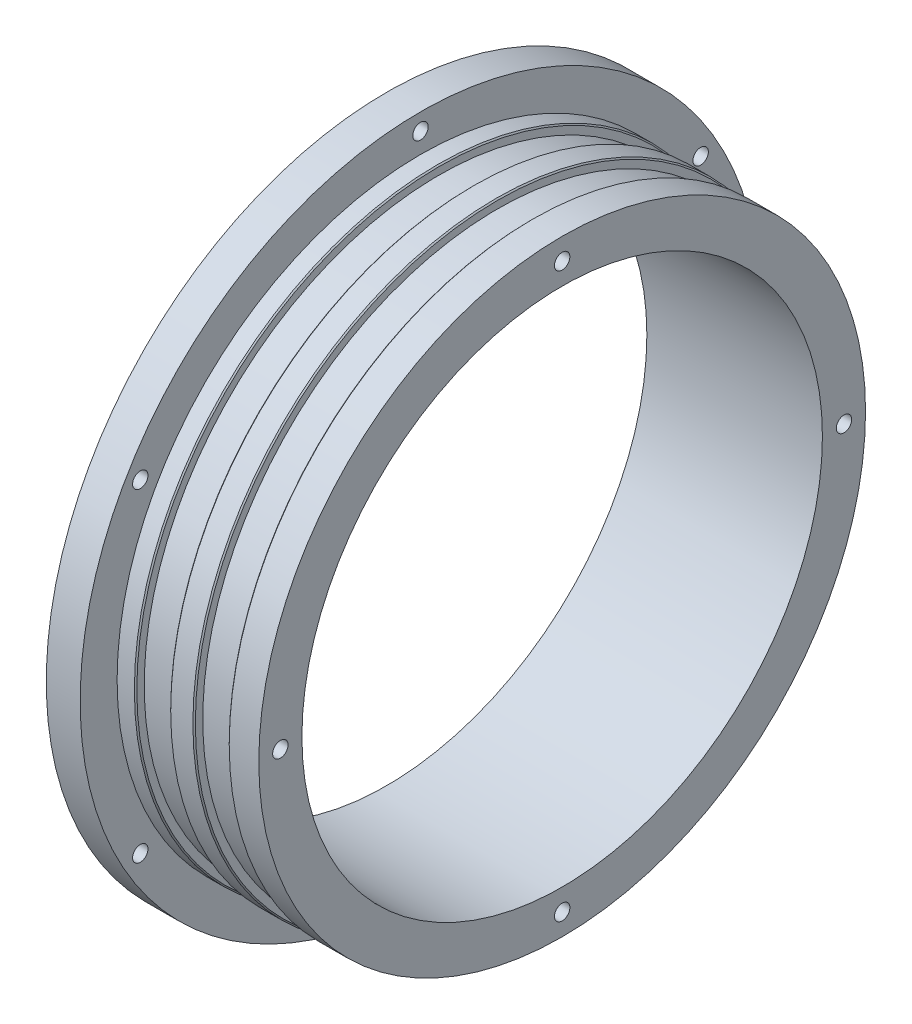
SolidWorks part; units mm, degrees
ref_plane "前视" through (0, 0, 0) normal (0, 0, 1) x (1, 0, 0)
ref_plane "上视" through (0, 0, 0) normal (0, 1, 0) x (1, 0, 0)
ref_plane "右视" through (0, 0, 0) normal (1, 0, 0) x (0, 0, -1)
sketch "草图2" plane through (0, 0, 0) normal (0, 1, 0) x (1, 0, 0)
  line L0 (0, 0) -> (-79.2417, 0) construction
  line L1 (-77.681, 55.25) -> (-72.181, 55.25)
  line L2 (-72.181, 55.25) -> (-72.181, 49.25)
  line L3 (-72.181, 49.25) -> (-69.181, 49.25)
  line L4 (-69.181, 49.25) -> (-69.181, 47.85)
  line L5 (-69.181, 47.85) -> (-63.681, 47.85)
  line L6 (-63.681, 47.85) -> (-63.681, 49.25)
  line L7 (-63.681, 49.25) -> (-59.681, 49.25)
  line L8 (-59.681, 49.25) -> (-59.681, 47.85)
  line L9 (-59.681, 47.85) -> (-54.181, 47.85)
  line L10 (-54.181, 47.85) -> (-54.181, 49.25)
  line L11 (-54.181, 49.25) -> (-49.181, 49.25)
  line L12 (-49.181, 49.25) -> (-49.181, 42.25)
  line L13 (-49.181, 42.25) -> (-77.681, 42.25)
  line L14 (-77.681, 42.25) -> (-77.681, 46.2)
  line L15 (-77.681, 46.2) -> (-76.781, 46.2)
  line L16 (-76.781, 46.2) -> (-76.781, 49.8)
  line L17 (-76.781, 49.8) -> (-77.681, 49.8)
  line L18 (-77.681, 49.8) -> (-77.681, 55.25)
  dimension "D1" = 5.5
  dimension "D2" = 28.5
  dimension "D3" = 6
  dimension "D4" = 1.4
  dimension "D5" = 1.4
  dimension "D6" = 1.4
  dimension "D7" = 1.4
  dimension "D8" = 5.5
  dimension "D9" = 5.5
  dimension "D10" = 3
  dimension "D11" = 4
  dimension "D12" = 5
  dimension "D13" = 0.9
  dimension "D14" = 3.6
  dimension "D15" = 5.45
  dimension "D16" = 49.25
  dimension "D17" = 55.25
  dimension "D18" = 7
  dimension "D19" = 42.25
  dimension "D20" = 3.95
revolve "旋转1" add sketch "草图2" angle 360 about L0
chamfer "倒角1" distance 0.2 angle 45 6 edges at (-77.681, 0, -46.2) (-77.681, 0, -49.8) (-69.181, 0, -49.25) (-63.681, 0, -49.25) (-59.681, 0, -49.25) (-54.181, 0, -49.25)
sketch "草图3" plane through (-49.181, 0, 0) normal (1, 0, 0) x (0, 0, -1)
  line L0 (0, 0) -> (0, 45.75) construction
  circle A0 centre (0, 0) radius 45.75
  circle A1 centre (0, 45.75) radius 1.5
  circle A2 centre (45.75, 0) radius 1.5
  circle A3 centre (0, -45.75) radius 1.5
  circle A4 centre (-45.75, 0) radius 1.5
  point P14 (0, 0)
  dimension "D2" = 4
  dimension "D1" = 45.75
hole_wizard "M3x0.5 螺纹孔2" positions "3D草图2" profile "草图5" tap size "M3x0.5" standard "ANSI Metric"
sketch3d "3D草图2"
  point P0 (-49.181, 45.75, 0)
sketch "草图5" plane through (-49.181, 45.75, 0) normal (0, 1, 0) x (0, 0, -1)
  line L0 (0, 0) -> (0, 4.7511)
  line L1 (0, 4.7511) -> (1.25, 4)
  line L2 (1.25, 4) -> (1.25, 0)
  line L5 (1.25, 0) -> (0, 0)
  line L10 (0, 4.7511) -> (-1.25, 4) construction
  line L11 (0, -6.35) -> (0, 107.95) construction
  dimension "螺纹孔钻头直径" = 2.5
  dimension "螺纹孔钻头深度" = 4
  dimension "导头角度" = 118
cosmetic thread "孔螺蚊线2" parameters "D1"=4, "D2"=3
hole_wizard "M3x0.5 螺纹孔3" positions "3D草图3" profile "草图9" tap size "M3x0.5" standard "ANSI Metric"
sketch3d "3D草图3"
  point P0 (-49.181, 0, -45.75)
  point P3 (-49.181, 0, 45.75)
  point P6 (-49.181, -45.75, 0)
sketch "草图9" plane through (-49.181, 0, -45.75) normal (0, 1, 0) x (0, 0, -1)
  line L0 (0, 0) -> (0, 4.7511)
  line L1 (0, 4.7511) -> (1.25, 4)
  line L2 (1.25, 4) -> (1.25, 0)
  line L5 (1.25, 0) -> (0, 0)
  line L10 (0, 4.7511) -> (-1.25, 4) construction
  line L11 (0, -6.35) -> (0, 107.95) construction
  dimension "螺纹孔钻头直径" = 2.5
  dimension "螺纹孔钻头深度" = 4
  dimension "导头角度" = 118
cosmetic thread "孔螺蚊线3" parameters "D1"=4, "D2"=3
cosmetic thread "孔螺蚊线4" parameters "D1"=4, "D2"=3
cosmetic thread "孔螺蚊线5" parameters "D1"=4, "D2"=3
sketch "草图10" plane through (-77.681, 0, 0) normal (-1, 0, 0) x (0, 0, 1)
  line L0 (0, 0) -> (0, 52.525) construction
  circle A0 centre (0, 0) radius 52.525
  circle A1 centre (0, 52.525) radius 1.5
  circle A2 centre (45.488, 26.2625) radius 1.5
  circle A3 centre (45.488, -26.2625) radius 1.5
  circle A4 centre (0, -52.525) radius 1.5
  circle A5 centre (-45.488, -26.2625) radius 1.5
  circle A6 centre (-45.488, 26.2625) radius 1.5
  point P19 (0, 0)
  dimension "D2" = 6
  dimension "D1" = 52.525
hole_wizard "M3x0.5 螺纹孔4" positions "3D草图4" profile "草图11" tap size "M3x0.5" standard "ANSI Metric" end condition through all
sketch3d "3D草图4"
  point P0 (-77.681, 52.525, 0)
  point P3 (-77.681, 26.2625, 45.488)
  point P6 (-77.681, -26.2625, 45.488)
  point P9 (-77.681, -52.525, 0)
  point P12 (-77.681, -26.2625, -45.488)
  point P15 (-77.681, 26.2625, -45.488)
sketch "草图11" plane through (-77.681, 52.525, 0) normal (0, 1, 0) x (0, 0, 1)
  line L0 (0, 0) -> (0, 28.5)
  line L1 (0, 28.5) -> (1.25, 28.5)
  line L2 (1.25, 28.5) -> (1.25, 0)
  line L5 (1.25, 0) -> (0, 0)
  line L11 (0, -6.35) -> (0, 107.95) construction
  dimension "通孔螺纹孔钻头直径" = 2.5
  dimension "通孔螺纹孔钻头深度" = 28.5
cosmetic thread "孔螺蚊线6" parameters "D2"=3
cosmetic thread "孔螺蚊线7" parameters "D2"=3
cosmetic thread "孔螺蚊线8" parameters "D2"=3
cosmetic thread "孔螺蚊线9" parameters "D2"=3
cosmetic thread "孔螺蚊线10" parameters "D2"=3
cosmetic thread "孔螺蚊线11" parameters "D2"=3
